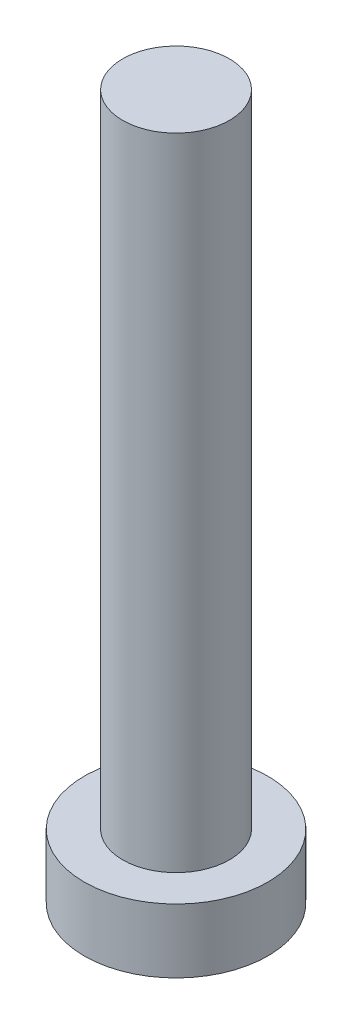
SolidWorks part; units mm, degrees
ref_plane "前视基准面" through (0, 0, 0) normal (0, 0, 1) x (1, 0, 0)
ref_plane "上视基准面" through (0, 0, 0) normal (0, 1, 0) x (1, 0, 0)
ref_plane "右视基准面" through (0, 0, 0) normal (1, 0, 0) x (0, 0, -1)
sketch "草图1" plane through (0, 0, 0) normal (0, 1, 0) x (1, 0, 0)
  circle A0 centre (0, 0) radius 4.3
extrude "凸台-拉伸1" add sketch "草图1" along normal blind 3
sketch "草图2" plane through (0, 3, 0) normal (0, 1, 0) x (1, 0, 0)
  circle A0 centre (0, 0) radius 2.5
extrude "凸台-拉伸2" add sketch "草图2" along normal blind 30
sketch "草图3" plane through (0, 0, 0) normal (0, -1, 0) x (1, 0, 0)
  line L0 (-0.6, 1.1) -> (-0.6, 2.4)
  line L1 (-2.4, -0.6) -> (-1.1, -0.6)
  line L2 (-2.4, -0.6) -> (-2.4, 0.6)
  line L3 (-2.4, 0.6) -> (-1.1, 0.6)
  line L4 (2.4, -0.6) -> (2.4, 0.6)
  line L5 (-2.4, -0.6) -> (2.4, 0.6) construction
  line L6 (-2.4, 0.6) -> (2.4, -0.6) construction
  line L7 (-0.6, -2.4) -> (0.6, -2.4)
  line L8 (-0.6, -2.4) -> (-0.6, -1.1)
  line L9 (-0.6, 2.4) -> (0.6, 2.4)
  line L10 (0.6, -2.4) -> (0.6, -1.1)
  line L11 (-0.6, -2.4) -> (0.6, 2.4) construction
  line L12 (-0.6, 2.4) -> (0.6, -2.4) construction
  line L13 (1.1, -0.6) -> (2.4, -0.6)
  line L14 (0.6, 1.1) -> (0.6, 2.4)
  line L15 (1.1, 0.6) -> (2.4, 0.6)
  arc A0 (-0.6, -1.1) -> (-1.1, -0.6) centre (-1.1, -1.1) ccw
  arc A1 (1.1, -0.6) -> (0.6, -1.1) centre (1.1, -1.1) ccw
  arc A2 (0.6, 1.1) -> (1.1, 0.6) centre (1.1, 1.1) ccw
  arc A3 (-0.6, 1.1) -> (-1.1, 0.6) centre (-1.1, 1.1) cw
  point P0 (0, 0)
  point P6 (0, 0)
  point P21 (0.6, 0.6)
  dimension "D1" = 0.5
extrude "切除-拉伸1" cut sketch "草图3" against normal blind 1.5
